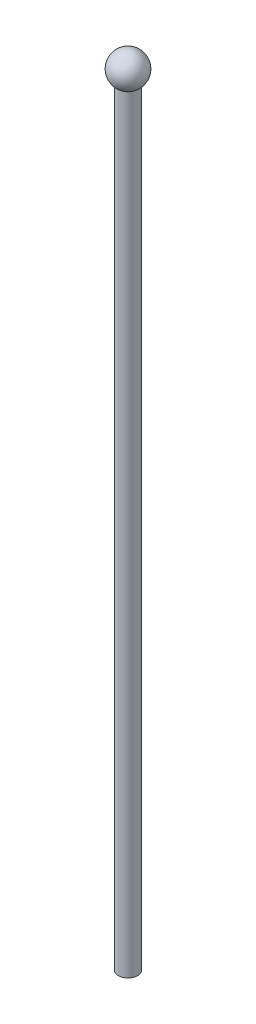
SolidWorks part; units mm, degrees
ref_plane "Front Plane" through (0, 0, 0) normal (0, 0, 1) x (1, 0, 0)
ref_plane "Top Plane" through (0, 0, 0) normal (0, 1, 0) x (1, 0, 0)
ref_plane "Right Plane" through (0, 0, 0) normal (1, 0, 0) x (0, 0, -1)
sketch "Sketch2" plane through (0, 0, 0) normal (0, 1, 0) x (1, 0, 0)
  circle A0 centre (0, 0) radius 3.175
  dimension "D1" = 6.35
extrude "Boss-Extrude1" add sketch "Sketch2" along normal blind 254
sketch "Sketch3" plane through (0, 0, 0) normal (0, 0, 1) x (1, 0, 0)
  line L0 (0, 252.9599) -> (0, 263.6917)
  arc A0 (0, 263.6917) -> (0, 252.9599) centre (0, 258.3258) ccw
revolve "Revolve1" add sketch "Sketch3" angle 360 about L0
